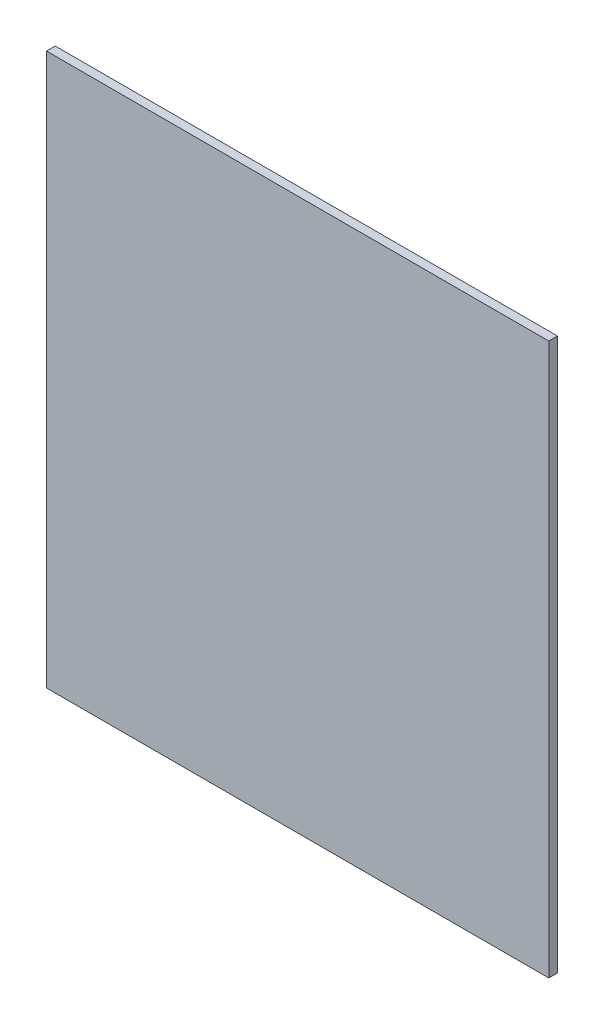
SolidWorks part; units mm, degrees
ref_plane "Plan de face" through (0, 0, 0) normal (0, 0, 1) x (1, 0, 0)
ref_plane "Plan de dessus" through (0, 0, 0) normal (0, 1, 0) x (1, 0, 0)
ref_plane "Plan de droite" through (0, 0, 0) normal (1, 0, 0) x (0, 0, -1)
sketch "Esquisse1" plane through (0, 0, 0) normal (0, 0, 1) x (1, 0, 0)
  line L1 (262.8393, 35.5513) -> (435.8393, 35.5513)
  line L2 (262.8393, 35.5513) -> (262.8393, -154.4487)
  line L3 (262.8393, -154.4487) -> (435.8393, -154.4487)
  line L4 (435.8393, 35.5513) -> (435.8393, -154.4487)
  dimension "D2" = 173
  dimension "D3" = 190
extrude "Boss.-Extru.1" add sketch "Esquisse1" along normal blind 3
equation "\"D3@Esquisse1\"= \"HauteurSyphon\" - ( \"HauteurCoteGauche\" - \"HauteurCoteDroit\" )"
equation "\"ProfondeurBoite\"=460"
equation "\"LongueurSyphon\"=170"
equation "\"LargeurSyphon\"=120"
equation "\"EpaisseurPlaque\"= 3"
equation "\"HauteurSyphon\"=\"HauteurCoteGauche\"-\"HauteurSolSyphon\""
equation "\"HauteurCoteDroit\"= 490"
equation "\"HauteurCoteGauche\"= 540"
equation "\"HauteurSolSyphon\"= 300"
equation "\"D2@Esquisse1\"= \"LongueurSyphon\" + \"EpaisseurPlaque\""
equation "\"LargeurDroite\"=10"
equation "\"LargeurGauche\"=150"
equation "\"LargeurBoite\"= \"LargeurDroite\" + \"LargeurGauche\" + \"LargeurSyphon\""
